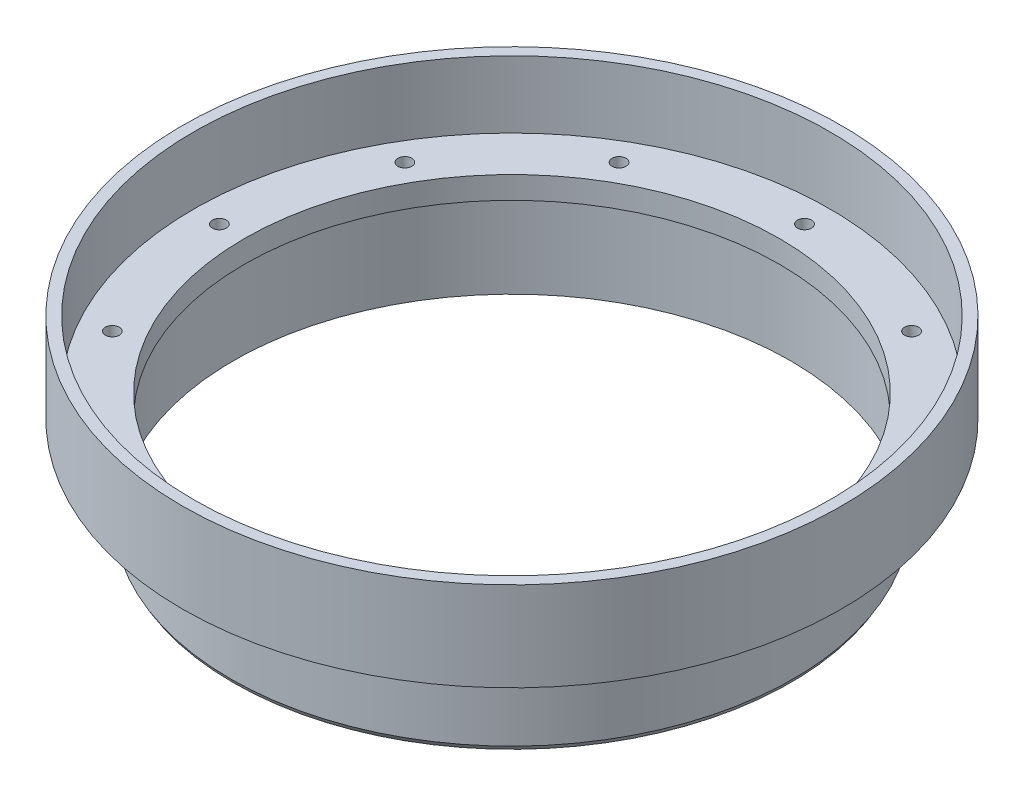
SolidWorks part; units mm, degrees
material "6061-T6 (SS)"
ref_plane "Front Plane" through (0, 0, 0) normal (0, 0, 1) x (1, 0, 0)
ref_plane "Top Plane" through (0, 0, 0) normal (0, 1, 0) x (1, 0, 0)
ref_plane "Right Plane" through (0, 0, 0) normal (1, 0, 0) x (0, 0, -1)
ref_axis "Axis1" through (0, 55, 0) along (0, -1, 0)
sketch "Cross Section" plane through (0, 0, 0) normal (0, 0, 1) x (1, 0, 0)
  line L0 (-38.1, 0) -> (-38.1, -3.175)
  line L1 (-38.1, -3.175) -> (-39.6875, -3.175)
  line L2 (-39.6875, -3.175) -> (-39.6875, -15.875)
  line L3 (-39.6875, -15.875) -> (-40.0685, -15.2151)
  line L4 (0, -15.875) -> (-38.1, -15.875) construction
  line L5 (-40.0685, -15.2151) -> (-40.0685, -3.175)
  line L6 (-40.0685, -3.175) -> (-46.9265, -3.175)
  line L7 (-46.9265, -3.175) -> (-46.9265, 9.525)
  line L8 (-46.9265, 9.525) -> (-45.339, 9.525)
  line L9 (-45.339, 9.525) -> (-45.339, 0)
  line L10 (-45.339, 0) -> (-38.1, 0)
  line L11 (-38.1, 0) -> (0, 0) construction
  line L12 (0, 55) -> (0, -55) construction
  dimension "D1" = 1.5875
  dimension "D3" = 0.381
  dimension "D4" = 30
  dimension "D5" = 6.858
  dimension "D6" = 12.7
  dimension "D9" = 3.175
  dimension "D8" = 38.1
  dimension "D2" = 1.5875
revolve "Main" add sketch "Cross Section" angle 360 about axis through (0, 55, 0) along (0, -1, 0)
sketch "Hole Location" plane through (0, 0, 0) normal (0, 1, 0) x (1, 0, 0)
  line L0 (0, 0) -> (-41.656, 0) construction
  circle A0 centre (0, 0) radius 41.656 construction
  dimension "D1" = 83.312
hole_wizard "#3-48 Tapped Hole1" positions "Sketch5" profile "Sketch7" tap size "#3-48" standard "ANSI Inch"
sketch "Sketch5" plane through (0, 0, 0) normal (0, 1, 0) x (1, 0, 0)
  point P0 (-41.656, 0)
sketch "Sketch7" plane through (-41.656, 0, 0) normal (1, 0, 0) x (0, 0, 1)
  line L0 (0, 0) -> (0, 3.901)
  line L1 (0, 3.901) -> (0.9969, 3.302)
  line L2 (0.9969, 3.302) -> (0.9969, 0)
  line L5 (0.9969, 0) -> (0, 0)
  line L10 (0, 3.901) -> (-0.997, 3.302) construction
  line L11 (0, -6.35) -> (0, 107.95) construction
  dimension "Tap Drill Dia." = 1.9939
  dimension "Tap Drill Depth" = 3.302
  dimension "Drill Angle" = 118
cosmetic thread "Hole Thread1" parameters "D1"=3.175, "D2"=2.5146
pattern_circular "Screw Holes" count 12 over 360 about axis through (0, 0, 0) along (0, 1, 0) of "#3-48 Tapped Hole1"
equation "\"D8@Cross Section\"=\"TANK DIAMETER@Cryo Tank.Assembly\"/2"
equation "\"D1@Hole Location\"=\"TANK DIAMETER@Cryo Tank.Assembly\"+\"GASKET SEAT THICKNESS@Cryo Tank.Assembly\""
equation "\"D1@Cross Section\"=\"LINER THICKNESS@Cryo Tank.Assembly\""
equation "\"D3@Cross Section\"=\"ALUMINUM LAP THICKNESS@Cryo Tank.Assembly\""
equation "\"D5@Cross Section\"=2*\"CF THICKNESS@Cryo Tank.Assembly\"+\"NOMEX THICKNESS@Cryo Tank.Assembly\""
